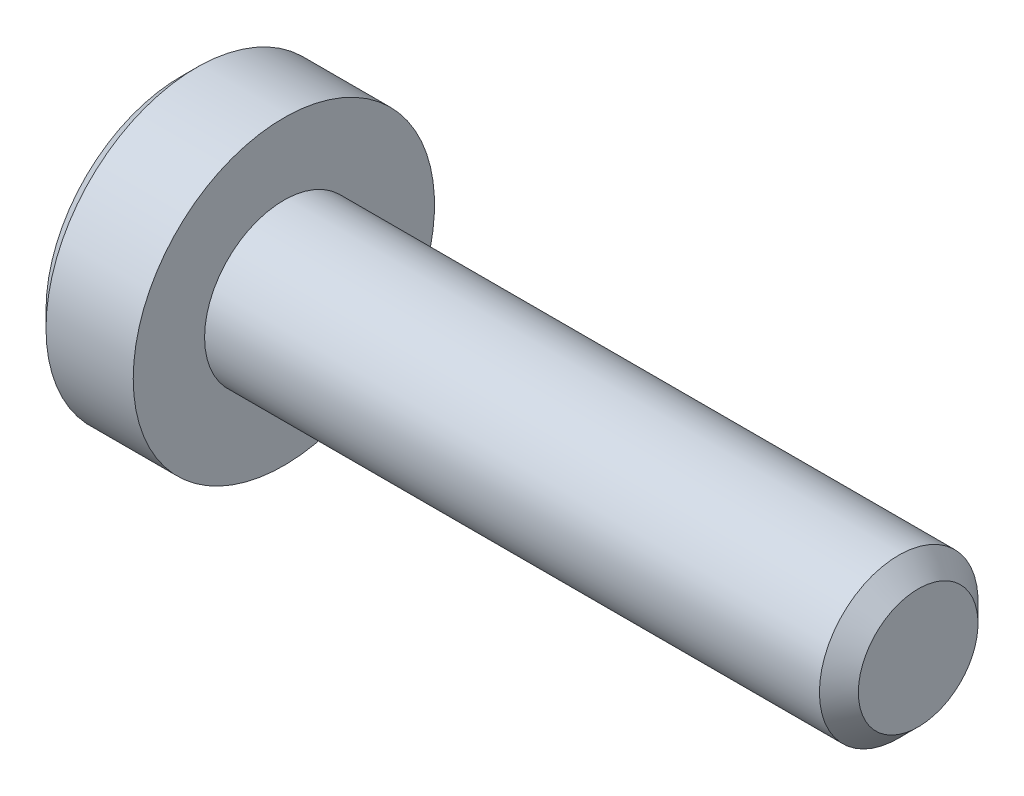
SolidWorks part; units mm, degrees
material "AISI 304"
ref_plane "正面" through (0, 0, 0) normal (0, 0, 1) x (1, 0, 0)
ref_plane "平面" through (0, 0, 0) normal (0, 1, 0) x (1, 0, 0)
ref_plane "右側面" through (0, 0, 0) normal (1, 0, 0) x (0, 0, -1)
ref_plane "Plane1" through (0, 0, 0) normal (0, 0, 1) x (1, 0, 0)
sketch "Sketch1" plane through (0, 0, 0) normal (0, 0, 1) x (1, 0, 0)
  line L0 (-1.3, 0) -> (-1.3, 1.7)
  line L1 (-1.3, 1.7) -> (-1.1, 1.9)
  line L2 (-1.1, 1.9) -> (0, 1.9)
  line L3 (0, 1.9) -> (0, 1)
  line L4 (0, 1) -> (7.7545, 1)
  line L5 (7.7545, 1) -> (8, 0.7545)
  line L6 (8, 0.7545) -> (8, 0)
  line L7 (8, 0) -> (-1.3, 0)
  line L8 (8, 0) -> (-1.3, 0) construction
revolve "Revolve1" add sketch "Sketch1" angle 360 about L8
cosmetic thread "Cosmetic Thread1" parameters "D1"=7.5748, "D2"=1.509
ref_plane "Plane2" through (-1.3, 0, 0) normal (1, 0, 0) x (0, 0, -1)
sketch "Sketch2" plane through (-1.3, 0, 0) normal (1, 0, 0) x (0, 0, -1)
  line L0 (-0.65, -0.3753) -> (0, -0.7506)
  line L1 (0, -0.7506) -> (0.65, -0.3753)
  line L2 (0.65, -0.3753) -> (0.65, 0.3753)
  line L3 (0.65, 0.3753) -> (0, 0.7506)
  line L4 (0, 0.7506) -> (-0.65, 0.3753)
  line L5 (-0.65, 0.3753) -> (-0.65, -0.3753)
extrude "Cut-Extrude1" cut sketch "Sketch2" along normal blind 0.7
